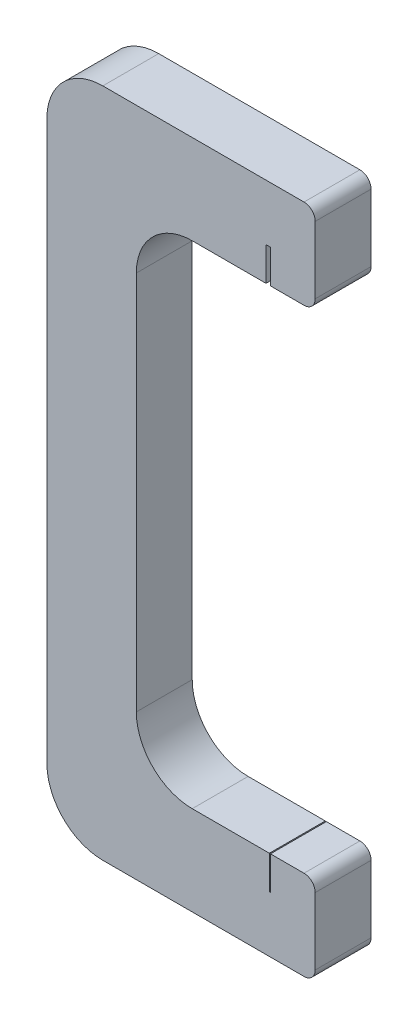
SolidWorks part; units mm, degrees
ref_plane "Front Plane" through (0, 0, 0) normal (0, 0, 1) x (1, 0, 0)
ref_plane "Top Plane" through (0, 0, 0) normal (0, 1, 0) x (1, 0, 0)
ref_plane "Right Plane" through (0, 0, 0) normal (1, 0, 0) x (0, 0, -1)
sketch "Sketch1" plane through (0, 0, 0) normal (0, 0, 1) x (1, 0, 0)
  line L0 (0, 55) -> (0, 5)
  line L1 (5, 0) -> (23, 0)
  line L2 (24, 1) -> (24, 7)
  line L3 (23, 8) -> (13, 8)
  line L4 (8, 13) -> (8, 47)
  line L5 (13, 52) -> (23, 52)
  line L6 (24, 53) -> (24, 59)
  line L7 (23, 60) -> (5, 60)
  arc A0 (5, 60) -> (0, 55) centre (5, 55) ccw
  arc A1 (13, 52) -> (8, 47) centre (13, 47) ccw
  arc A2 (13, 8) -> (8, 13) centre (13, 13) cw
  arc A3 (5, 0) -> (0, 5) centre (5, 5) cw
  arc A4 (24, 59) -> (23, 60) centre (23, 59) ccw
  arc A5 (24, 53) -> (23, 52) centre (23, 53) cw
  arc A6 (24, 1) -> (23, 0) centre (23, 1) cw
  arc A7 (24, 7) -> (23, 8) centre (23, 7) ccw
  point P11 (0, 60)
  point P18 (0, 0)
  point P21 (24, 60)
  point P24 (24, 52)
  point P27 (24, 0)
  point P30 (24, 8)
  dimension "D6" = 5
  dimension "D7" = 5
  dimension "D8" = 5
  dimension "D9" = 5
  dimension "D10" = 1
  dimension "D1" = 60
  dimension "D2" = 8
  dimension "D3" = 8
  dimension "D4" = 16
  dimension "D5" = 8
extrude "Boss-Extrude1" add sketch "Sketch1" along normal blind 5
sketch "Sketch3" plane through (0, 8, 0) normal (0, 1, 0) x (1, 0, 0)
  line L0 (0, -2.5) -> (19.95, -2.5) construction
  line L1 (0, -5) -> (0, 0) construction
  line L2 (23, 0) -> (13, 0) construction
  line L3 (19.9, -5) -> (20, -5)
  line L4 (19.9, -5) -> (19.9, 0)
  line L5 (19.9, 0) -> (20, 0)
  line L6 (20, -5) -> (20, 0)
  line L7 (19.9, -5) -> (20, 0) construction
  line L8 (19.9, 0) -> (20, -5) construction
  dimension "D1" = 19.95
  dimension "D2" = 0.1
extrude "Cut-Extrude1" cut sketch "Sketch3" against normal blind 3
sketch "Sketch4" plane through (0, 52, 0) normal (0, -1, 0) x (1, 0, 0)
  line L0 (0, 2.5) -> (19.8, 2.5) construction
  line L1 (0, 5) -> (0, 0) construction
  line L2 (13, 5) -> (23, 5) construction
  line L3 (19.6, 0) -> (20, 0)
  line L4 (19.6, 0) -> (19.6, 5)
  line L5 (19.6, 5) -> (20, 5)
  line L6 (20, 0) -> (20, 5)
  line L7 (19.6, 0) -> (20, 5) construction
  line L8 (19.6, 5) -> (20, 0) construction
  dimension "D1" = 19.8
  dimension "D2" = 0.4
extrude "Cut-Extrude2" cut sketch "Sketch4" against normal blind 3
equation "\"A.L\"= 0.07m"
equation "\"A.h\"= 0.007m"
equation "\"A.d\"= 0.005m"
equation "\"A.delta\"= 45.0001"
equation "\"A.w\"= 0m"
equation "\"A.v\"= 0.013m"
equation "\"A.s\"= 0.014m"
equation "\"A.t\"= 0.007m"
equation "\"B.L\"= 0.065m"
equation "\"B.h\"= 0.008m"
equation "\"B.s\"= 0.016m"
equation "\"B.t\"= 0.008m"
equation "\"C.h\"= 0.0065m"
equation "\"C.d\"= 0.005m"
equation "\"C.L\"= 0.05m"
equation "\"C.wmax\"= 0.003m"
equation "\"D.L\"= 0.06m"
equation "\"D.h\"= 0.008m"
equation "\"D.s\"= 0.012m"
equation "\"D.t\"= 0.008m"
equation "\"a_h\"= 0.0001m"
equation "\"a_d\"= 0.005m"
equation "\"a_L\"= 0.008m"
equation "\"b_h\"= 0.0004m"
equation "\"b_d\"= 0.005m"
equation "\"b_L\"= 0.008m"
equation "\"c_h\"= 0.0001m"
equation "\"c_d\"= 0.005m"
equation "\"c_L\"= 0.01m"
equation "\"d_h\"= 0.0001m"
equation "\"d_d\"= 0.005m"
equation "\"d_L\"= 0.01m"
equation "\"S.h\"= 0.015m"
equation "\"S.L\"= 0.09175m"
equation "\"D1@Sketch1\"=\"D.L\""
equation "\"D2@Sketch1\"=\"D.h\""
equation "\"D3@Sketch1\"=\"D.h\""
equation "\"D4@Sketch1\"=\"D.s\"+0.004"
equation "\"D5@Sketch1\"=\"D.h\""
equation "\"D1@Boss-Extrude1\"=\"A.d\""
equation "\"D1@Sketch3\"=\"D.h\"+\"D.s\"-\"a_h\"/2"
equation "\"D2@Sketch3\"=\"a_h\""
equation "\"D1@Sketch4\"=\"D.h\"+\"D.s\"-\"b_h\"/2"
equation "\"D2@Sketch4\"=\"b_h\""
